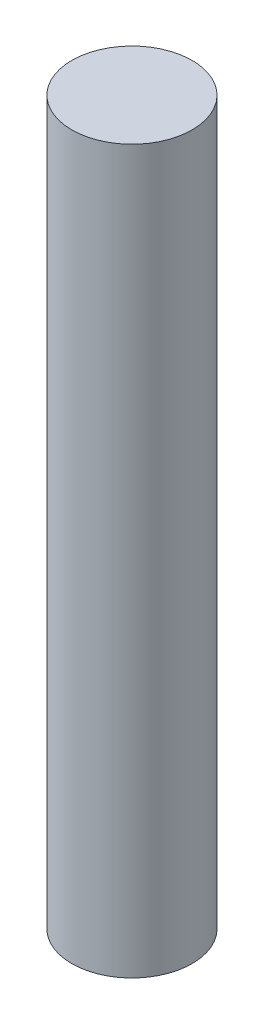
SolidWorks part; units mm, degrees
ref_plane "Front Plane" through (0, 0, 0) normal (0, 0, 1) x (1, 0, 0)
ref_plane "Top Plane" through (0, 0, 0) normal (0, 1, 0) x (1, 0, 0)
ref_plane "Right Plane" through (0, 0, 0) normal (1, 0, 0) x (0, 0, -1)
sketch "Sketch2" plane through (0, 0, 0) normal (0, 1, 0) x (1, 0, 0)
  circle A0 centre (0, 0) radius 15.875
  dimension "D1" = 31.75
extrude "Boss-Extrude1" add sketch "Sketch2" along normal blind 190.5
